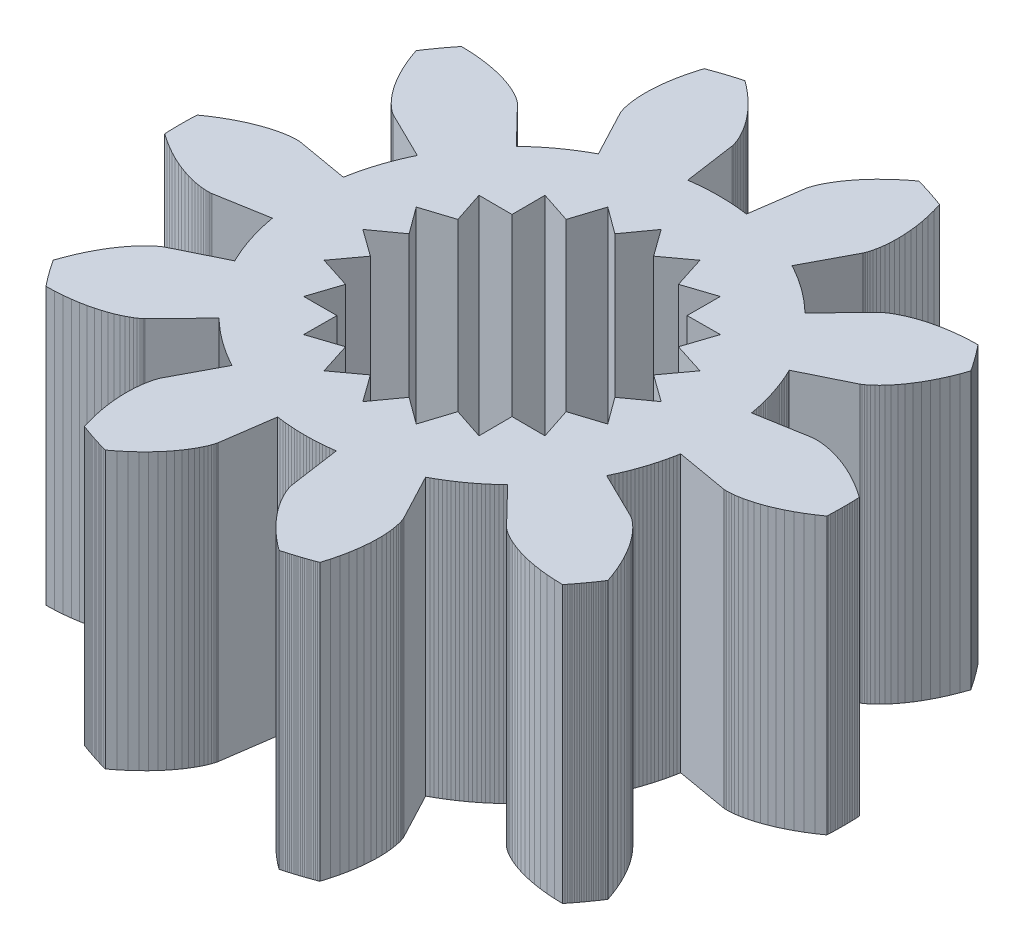
SolidWorks part; units mm, degrees
ref_plane "Front Plane" through (0, 0, 0) normal (0, 0, 1) x (1, 0, 0)
ref_plane "Top Plane" through (0, 0, 0) normal (0, 1, 0) x (1, 0, 0)
ref_plane "Right Plane" through (0, 0, 0) normal (1, 0, 0) x (0, 0, -1)
sketch "Sketch1" plane through (0, 0, 0) normal (0, 1, 0) x (1, 0, 0)
  line L0 (3.6947, -0.6418) -> (4.6291, -0.8041)
  line L1 (4.6291, -0.8041) -> (4.6332, -0.8047)
  line L2 (4.6332, -0.8047) -> (4.6455, -0.806)
  line L3 (4.6455, -0.806) -> (4.6659, -0.8073)
  line L4 (4.6659, -0.8073) -> (4.6947, -0.8081)
  line L5 (4.6947, -0.8081) -> (4.7316, -0.8074)
  line L6 (4.7316, -0.8074) -> (4.7767, -0.8048)
  line L7 (4.7767, -0.8048) -> (4.8297, -0.7994)
  line L8 (4.8297, -0.7994) -> (4.8907, -0.7907)
  line L9 (4.8907, -0.7907) -> (4.9593, -0.778)
  line L10 (4.9593, -0.778) -> (5.0353, -0.7605)
  line L11 (5.0353, -0.7605) -> (5.1184, -0.7378)
  line L12 (5.1184, -0.7378) -> (5.2084, -0.7091)
  line L13 (5.2084, -0.7091) -> (5.3047, -0.6738)
  line L14 (5.3047, -0.6738) -> (5.4071, -0.6314)
  line L15 (5.4071, -0.6314) -> (5.5151, -0.5813)
  line L16 (5.5151, -0.5813) -> (5.6282, -0.523)
  line L17 (5.6282, -0.523) -> (5.7459, -0.456)
  line L18 (5.7459, -0.456) -> (5.8676, -0.3797)
  line L19 (5.8676, -0.3797) -> (5.9928, -0.2937)
  line L20 (5.9928, -0.2937) -> (5.9942, -0.2628)
  line L21 (5.9942, -0.2628) -> (5.9955, -0.2319)
  line L22 (5.9955, -0.2319) -> (5.9966, -0.201)
  line L23 (5.9966, -0.201) -> (5.9976, -0.1701)
  line L24 (5.9976, -0.1701) -> (5.9984, -0.1392)
  line L25 (5.9984, -0.1392) -> (5.999, -0.1083)
  line L26 (5.999, -0.1083) -> (5.9995, -0.0773)
  line L27 (5.9995, -0.0773) -> (5.9998, -0.0464)
  line L28 (5.9998, -0.0464) -> (6, -0.0155)
  line L29 (6, -0.0155) -> (6, 0.0155)
  line L30 (6, 0.0155) -> (5.9998, 0.0464)
  line L31 (5.9998, 0.0464) -> (5.9995, 0.0773)
  line L32 (5.9995, 0.0773) -> (5.999, 0.1083)
  line L33 (5.999, 0.1083) -> (5.9984, 0.1392)
  line L34 (5.9984, 0.1392) -> (5.9976, 0.1701)
  line L35 (5.9976, 0.1701) -> (5.9966, 0.201)
  line L36 (5.9966, 0.201) -> (5.9955, 0.2319)
  line L37 (5.9955, 0.2319) -> (5.9942, 0.2628)
  line L38 (5.9942, 0.2628) -> (5.9928, 0.2937)
  line L39 (5.9928, 0.2937) -> (5.8676, 0.3797)
  line L40 (5.8676, 0.3797) -> (5.7459, 0.456)
  line L41 (5.7459, 0.456) -> (5.6282, 0.523)
  line L42 (5.6282, 0.523) -> (5.5151, 0.5813)
  line L43 (5.5151, 0.5813) -> (5.4071, 0.6314)
  line L44 (5.4071, 0.6314) -> (5.3047, 0.6738)
  line L45 (5.3047, 0.6738) -> (5.2084, 0.7091)
  line L46 (5.2084, 0.7091) -> (5.1184, 0.7378)
  line L47 (5.1184, 0.7378) -> (5.0353, 0.7605)
  line L48 (5.0353, 0.7605) -> (4.9593, 0.778)
  line L49 (4.9593, 0.778) -> (4.8907, 0.7907)
  line L50 (4.8907, 0.7907) -> (4.8297, 0.7994)
  line L51 (4.8297, 0.7994) -> (4.7767, 0.8048)
  line L52 (4.7767, 0.8048) -> (4.7316, 0.8074)
  line L53 (4.7316, 0.8074) -> (4.6947, 0.8081)
  line L54 (4.6947, 0.8081) -> (4.6659, 0.8073)
  line L55 (4.6659, 0.8073) -> (4.6455, 0.806)
  line L56 (4.6455, 0.806) -> (4.6332, 0.8047)
  line L57 (4.6332, 0.8047) -> (4.6291, 0.8041)
  line L58 (4.6291, 0.8041) -> (3.6947, 0.6418)
  line L59 (3.6947, 0.6418) -> (3.6847, 0.697)
  line L60 (3.6847, 0.697) -> (3.6738, 0.752)
  line L61 (3.6738, 0.752) -> (3.6621, 0.8069)
  line L62 (3.6621, 0.8069) -> (3.6497, 0.8617)
  line L63 (3.6497, 0.8617) -> (3.6364, 0.9162)
  line L64 (3.6364, 0.9162) -> (3.6222, 0.9705)
  line L65 (3.6222, 0.9705) -> (3.6073, 1.0246)
  line L66 (3.6073, 1.0246) -> (3.5916, 1.0785)
  line L67 (3.5916, 1.0785) -> (3.575, 1.1321)
  line L68 (3.575, 1.1321) -> (3.5577, 1.1855)
  line L69 (3.5577, 1.1855) -> (3.5396, 1.2386)
  line L70 (3.5396, 1.2386) -> (3.5206, 1.2914)
  line L71 (3.5206, 1.2914) -> (3.5009, 1.344)
  line L72 (3.5009, 1.344) -> (3.4804, 1.3962)
  line L73 (3.4804, 1.3962) -> (3.4591, 1.4481)
  line L74 (3.4591, 1.4481) -> (3.4371, 1.4997)
  line L75 (3.4371, 1.4997) -> (3.4142, 1.551)
  line L76 (3.4142, 1.551) -> (3.3906, 1.6019)
  line L77 (3.3906, 1.6019) -> (3.3663, 1.6525)
  line L78 (3.3663, 1.6525) -> (4.2177, 2.0704)
  line L79 (4.2177, 2.0704) -> (4.2213, 2.0723)
  line L80 (4.2213, 2.0723) -> (4.232, 2.0785)
  line L81 (4.232, 2.0785) -> (4.2494, 2.0894)
  line L82 (4.2494, 2.0894) -> (4.273, 2.1057)
  line L83 (4.273, 2.1057) -> (4.3025, 2.1279)
  line L84 (4.3025, 2.1279) -> (4.3374, 2.1566)
  line L85 (4.3374, 2.1566) -> (4.3773, 2.1921)
  line L86 (4.3773, 2.1921) -> (4.4214, 2.235)
  line L87 (4.4214, 2.235) -> (4.4694, 2.2856)
  line L88 (4.4694, 2.2856) -> (4.5207, 2.3444)
  line L89 (4.5207, 2.3444) -> (4.5746, 2.4117)
  line L90 (4.5746, 2.4117) -> (4.6304, 2.4877)
  line L91 (4.6304, 2.4877) -> (4.6877, 2.5729)
  line L92 (4.6877, 2.5729) -> (4.7456, 2.6674)
  line L93 (4.7456, 2.6674) -> (4.8035, 2.7714)
  line L94 (4.8035, 2.7714) -> (4.8607, 2.885)
  line L95 (4.8607, 2.885) -> (4.9165, 3.0085)
  line L96 (4.9165, 3.0085) -> (4.9702, 3.1417)
  line L97 (4.9702, 3.1417) -> (5.0209, 3.2848)
  line L98 (5.0209, 3.2848) -> (5.0039, 3.3107)
  line L99 (5.0039, 3.3107) -> (4.9868, 3.3364)
  line L100 (4.9868, 3.3364) -> (4.9695, 3.3621)
  line L101 (4.9695, 3.3621) -> (4.9521, 3.3877)
  line L102 (4.9521, 3.3877) -> (4.9346, 3.4132)
  line L103 (4.9346, 3.4132) -> (4.9169, 3.4386)
  line L104 (4.9169, 3.4386) -> (4.8992, 3.4639)
  line L105 (4.8992, 3.4639) -> (4.8812, 3.4891)
  line L106 (4.8812, 3.4891) -> (4.8632, 3.5142)
  line L107 (4.8632, 3.5142) -> (4.845, 3.5392)
  line L108 (4.845, 3.5392) -> (4.8267, 3.5641)
  line L109 (4.8267, 3.5641) -> (4.8082, 3.589)
  line L110 (4.8082, 3.589) -> (4.7897, 3.6137)
  line L111 (4.7897, 3.6137) -> (4.771, 3.6384)
  line L112 (4.771, 3.6384) -> (4.7522, 3.6629)
  line L113 (4.7522, 3.6629) -> (4.7332, 3.6874)
  line L114 (4.7332, 3.6874) -> (4.7141, 3.7117)
  line L115 (4.7141, 3.7117) -> (4.6949, 3.736)
  line L116 (4.6949, 3.736) -> (4.6756, 3.7601)
  line L117 (4.6756, 3.7601) -> (4.5238, 3.7561)
  line L118 (4.5238, 3.7561) -> (4.3805, 3.7462)
  line L119 (4.3805, 3.7462) -> (4.2459, 3.7313)
  line L120 (4.2459, 3.7313) -> (4.1201, 3.712)
  line L121 (4.1201, 3.712) -> (4.0033, 3.6891)
  line L122 (4.0033, 3.6891) -> (3.8956, 3.6632)
  line L123 (3.8956, 3.6632) -> (3.7969, 3.6351)
  line L124 (3.7969, 3.6351) -> (3.7072, 3.6054)
  line L125 (3.7072, 3.6054) -> (3.6266, 3.575)
  line L126 (3.6266, 3.575) -> (3.5549, 3.5444)
  line L127 (3.5549, 3.5444) -> (3.4919, 3.5144)
  line L128 (3.4919, 3.5144) -> (3.4374, 3.4856)
  line L129 (3.4374, 3.4856) -> (3.3914, 3.4587)
  line L130 (3.3914, 3.4587) -> (3.3533, 3.4344)
  line L131 (3.3533, 3.4344) -> (3.3231, 3.4132)
  line L132 (3.3231, 3.4132) -> (3.3003, 3.3957)
  line L133 (3.3003, 3.3957) -> (3.2845, 3.3826)
  line L134 (3.2845, 3.3826) -> (3.2754, 3.3743)
  line L135 (3.2754, 3.3743) -> (3.2724, 3.3715)
  line L136 (3.2724, 3.3715) -> (2.6118, 2.6909)
  line L137 (2.6118, 2.6909) -> (2.5713, 2.7297)
  line L138 (2.5713, 2.7297) -> (2.5301, 2.7678)
  line L139 (2.5301, 2.7678) -> (2.4884, 2.8054)
  line L140 (2.4884, 2.8054) -> (2.4462, 2.8423)
  line L141 (2.4462, 2.8423) -> (2.4034, 2.8786)
  line L142 (2.4034, 2.8786) -> (2.36, 2.9142)
  line L143 (2.36, 2.9142) -> (2.3161, 2.9492)
  line L144 (2.3161, 2.9492) -> (2.2717, 2.9836)
  line L145 (2.2717, 2.9836) -> (2.2268, 3.0172)
  line L146 (2.2268, 3.0172) -> (2.1814, 3.0502)
  line L147 (2.1814, 3.0502) -> (2.1355, 3.0825)
  line L148 (2.1355, 3.0825) -> (2.0892, 3.1141)
  line L149 (2.0892, 3.1141) -> (2.0423, 3.1451)
  line L150 (2.0423, 3.1451) -> (1.995, 3.1753)
  line L151 (1.995, 3.1753) -> (1.9473, 3.2048)
  line L152 (1.9473, 3.2048) -> (1.8991, 3.2336)
  line L153 (1.8991, 3.2336) -> (1.8505, 3.2616)
  line L154 (1.8505, 3.2616) -> (1.8015, 3.2889)
  line L155 (1.8015, 3.2889) -> (1.7521, 3.3155)
  line L156 (1.7521, 3.3155) -> (2.1952, 4.1541)
  line L157 (2.1952, 4.1541) -> (2.197, 4.1578)
  line L158 (2.197, 4.1578) -> (2.2021, 4.169)
  line L159 (2.2021, 4.169) -> (2.2097, 4.1881)
  line L160 (2.2097, 4.1881) -> (2.2192, 4.2152)
  line L161 (2.2192, 4.2152) -> (2.23, 4.2505)
  line L162 (2.23, 4.2505) -> (2.2415, 4.2942)
  line L163 (2.2415, 4.2942) -> (2.2528, 4.3463)
  line L164 (2.2528, 4.3463) -> (2.2633, 4.407)
  line L165 (2.2633, 4.407) -> (2.2724, 4.4762)
  line L166 (2.2724, 4.4762) -> (2.2793, 4.5538)
  line L167 (2.2793, 4.5538) -> (2.2834, 4.6399)
  line L168 (2.2834, 4.6399) -> (2.2838, 4.7343)
  line L169 (2.2838, 4.7343) -> (2.2801, 4.8369)
  line L170 (2.2801, 4.8369) -> (2.2714, 4.9474)
  line L171 (2.2714, 4.9474) -> (2.2571, 5.0655)
  line L172 (2.2571, 5.0655) -> (2.2366, 5.1911)
  line L173 (2.2366, 5.1911) -> (2.2092, 5.3237)
  line L174 (2.2092, 5.3237) -> (2.1743, 5.4631)
  line L175 (2.1743, 5.4631) -> (2.1312, 5.6087)
  line L176 (2.1312, 5.6087) -> (2.1023, 5.6196)
  line L177 (2.1023, 5.6196) -> (2.0733, 5.6304)
  line L178 (2.0733, 5.6304) -> (2.0442, 5.641)
  line L179 (2.0442, 5.641) -> (2.0151, 5.6515)
  line L180 (2.0151, 5.6515) -> (1.986, 5.6618)
  line L181 (1.986, 5.6618) -> (1.9568, 5.672)
  line L182 (1.9568, 5.672) -> (1.9275, 5.682)
  line L183 (1.9275, 5.682) -> (1.8982, 5.6918)
  line L184 (1.8982, 5.6918) -> (1.8688, 5.7015)
  line L185 (1.8688, 5.7015) -> (1.8394, 5.7111)
  line L186 (1.8394, 5.7111) -> (1.8099, 5.7205)
  line L187 (1.8099, 5.7205) -> (1.7804, 5.7298)
  line L188 (1.7804, 5.7298) -> (1.7508, 5.7389)
  line L189 (1.7508, 5.7389) -> (1.7212, 5.7478)
  line L190 (1.7212, 5.7478) -> (1.6916, 5.7566)
  line L191 (1.6916, 5.7566) -> (1.6619, 5.7653)
  line L192 (1.6619, 5.7653) -> (1.6321, 5.7737)
  line L193 (1.6321, 5.7737) -> (1.6023, 5.7821)
  line L194 (1.6023, 5.7821) -> (1.5725, 5.7903)
  line L195 (1.5725, 5.7903) -> (1.4521, 5.6977)
  line L196 (1.4521, 5.6977) -> (1.3419, 5.6055)
  line L197 (1.3419, 5.6055) -> (1.2418, 5.5143)
  line L198 (1.2418, 5.5143) -> (1.1514, 5.4248)
  line L199 (1.1514, 5.4248) -> (1.0704, 5.3376)
  line L200 (1.0704, 5.3376) -> (0.9984, 5.2533)
  line L201 (0.9984, 5.2533) -> (0.9351, 5.1726)
  line L202 (0.9351, 5.1726) -> (0.88, 5.0959)
  line L203 (0.88, 5.0959) -> (0.8327, 5.0239)
  line L204 (0.8327, 5.0239) -> (0.7926, 4.957)
  line L205 (0.7926, 4.957) -> (0.7593, 4.8957)
  line L206 (0.7593, 4.8957) -> (0.7322, 4.8404)
  line L207 (0.7322, 4.8404) -> (0.7107, 4.7916)
  line L208 (0.7107, 4.7916) -> (0.6942, 4.7495)
  line L209 (0.6942, 4.7495) -> (0.6822, 4.7146)
  line L210 (0.6822, 4.7146) -> (0.674, 4.687)
  line L211 (0.674, 4.687) -> (0.669, 4.6672)
  line L212 (0.669, 4.6672) -> (0.6665, 4.6551)
  line L213 (0.6665, 4.6551) -> (0.6658, 4.6511)
  line L214 (0.6658, 4.6511) -> (0.5314, 3.7122)
  line L215 (0.5314, 3.7122) -> (0.4757, 3.7197)
  line L216 (0.4757, 3.7197) -> (0.42, 3.7264)
  line L217 (0.42, 3.7264) -> (0.3642, 3.7323)
  line L218 (0.3642, 3.7323) -> (0.3083, 3.7373)
  line L219 (0.3083, 3.7373) -> (0.2524, 3.7415)
  line L220 (0.2524, 3.7415) -> (0.1963, 3.7449)
  line L221 (0.1963, 3.7449) -> (0.1403, 3.7474)
  line L222 (0.1403, 3.7474) -> (0.0842, 3.7491)
  line L223 (0.0842, 3.7491) -> (0.0281, 3.7499)
  line L224 (0.0281, 3.7499) -> (-0.0281, 3.7499)
  line L225 (-0.0281, 3.7499) -> (-0.0842, 3.7491)
  line L226 (-0.0842, 3.7491) -> (-0.1403, 3.7474)
  line L227 (-0.1403, 3.7474) -> (-0.1963, 3.7449)
  line L228 (-0.1963, 3.7449) -> (-0.2524, 3.7415)
  line L229 (-0.2524, 3.7415) -> (-0.3083, 3.7373)
  line L230 (-0.3083, 3.7373) -> (-0.3642, 3.7323)
  line L231 (-0.3642, 3.7323) -> (-0.42, 3.7264)
  line L232 (-0.42, 3.7264) -> (-0.4757, 3.7197)
  line L233 (-0.4757, 3.7197) -> (-0.5314, 3.7122)
  line L234 (-0.5314, 3.7122) -> (-0.6658, 4.6511)
  line L235 (-0.6658, 4.6511) -> (-0.6665, 4.6551)
  line L236 (-0.6665, 4.6551) -> (-0.669, 4.6672)
  line L237 (-0.669, 4.6672) -> (-0.674, 4.687)
  line L238 (-0.674, 4.687) -> (-0.6822, 4.7146)
  line L239 (-0.6822, 4.7146) -> (-0.6942, 4.7495)
  line L240 (-0.6942, 4.7495) -> (-0.7107, 4.7916)
  line L241 (-0.7107, 4.7916) -> (-0.7322, 4.8404)
  line L242 (-0.7322, 4.8404) -> (-0.7593, 4.8957)
  line L243 (-0.7593, 4.8957) -> (-0.7926, 4.957)
  line L244 (-0.7926, 4.957) -> (-0.8327, 5.0239)
  line L245 (-0.8327, 5.0239) -> (-0.88, 5.0959)
  line L246 (-0.88, 5.0959) -> (-0.9351, 5.1726)
  line L247 (-0.9351, 5.1726) -> (-0.9984, 5.2533)
  line L248 (-0.9984, 5.2533) -> (-1.0704, 5.3376)
  line L249 (-1.0704, 5.3376) -> (-1.1514, 5.4248)
  line L250 (-1.1514, 5.4248) -> (-1.2418, 5.5143)
  line L251 (-1.2418, 5.5143) -> (-1.3419, 5.6055)
  line L252 (-1.3419, 5.6055) -> (-1.4521, 5.6977)
  line L253 (-1.4521, 5.6977) -> (-1.5725, 5.7903)
  line L254 (-1.5725, 5.7903) -> (-1.6023, 5.7821)
  line L255 (-1.6023, 5.7821) -> (-1.6321, 5.7737)
  line L256 (-1.6321, 5.7737) -> (-1.6619, 5.7653)
  line L257 (-1.6619, 5.7653) -> (-1.6916, 5.7566)
  line L258 (-1.6916, 5.7566) -> (-1.7212, 5.7478)
  line L259 (-1.7212, 5.7478) -> (-1.7508, 5.7389)
  line L260 (-1.7508, 5.7389) -> (-1.7804, 5.7298)
  line L261 (-1.7804, 5.7298) -> (-1.8099, 5.7205)
  line L262 (-1.8099, 5.7205) -> (-1.8394, 5.7111)
  line L263 (-1.8394, 5.7111) -> (-1.8688, 5.7015)
  line L264 (-1.8688, 5.7015) -> (-1.8982, 5.6918)
  line L265 (-1.8982, 5.6918) -> (-1.9275, 5.682)
  line L266 (-1.9275, 5.682) -> (-1.9568, 5.672)
  line L267 (-1.9568, 5.672) -> (-1.986, 5.6618)
  line L268 (-1.986, 5.6618) -> (-2.0151, 5.6515)
  line L269 (-2.0151, 5.6515) -> (-2.0442, 5.641)
  line L270 (-2.0442, 5.641) -> (-2.0733, 5.6304)
  line L271 (-2.0733, 5.6304) -> (-2.1023, 5.6196)
  line L272 (-2.1023, 5.6196) -> (-2.1312, 5.6087)
  line L273 (-2.1312, 5.6087) -> (-2.1743, 5.4631)
  line L274 (-2.1743, 5.4631) -> (-2.2092, 5.3237)
  line L275 (-2.2092, 5.3237) -> (-2.2366, 5.1911)
  line L276 (-2.2366, 5.1911) -> (-2.2571, 5.0655)
  line L277 (-2.2571, 5.0655) -> (-2.2714, 4.9474)
  line L278 (-2.2714, 4.9474) -> (-2.2801, 4.8369)
  line L279 (-2.2801, 4.8369) -> (-2.2838, 4.7343)
  line L280 (-2.2838, 4.7343) -> (-2.2834, 4.6399)
  line L281 (-2.2834, 4.6399) -> (-2.2793, 4.5538)
  line L282 (-2.2793, 4.5538) -> (-2.2724, 4.4762)
  line L283 (-2.2724, 4.4762) -> (-2.2633, 4.407)
  line L284 (-2.2633, 4.407) -> (-2.2528, 4.3463)
  line L285 (-2.2528, 4.3463) -> (-2.2415, 4.2942)
  line L286 (-2.2415, 4.2942) -> (-2.23, 4.2505)
  line L287 (-2.23, 4.2505) -> (-2.2192, 4.2152)
  line L288 (-2.2192, 4.2152) -> (-2.2097, 4.1881)
  line L289 (-2.2097, 4.1881) -> (-2.2021, 4.169)
  line L290 (-2.2021, 4.169) -> (-2.197, 4.1578)
  line L291 (-2.197, 4.1578) -> (-2.1952, 4.1541)
  line L292 (-2.1952, 4.1541) -> (-1.7521, 3.3155)
  line L293 (-1.7521, 3.3155) -> (-1.8015, 3.2889)
  line L294 (-1.8015, 3.2889) -> (-1.8505, 3.2616)
  line L295 (-1.8505, 3.2616) -> (-1.8991, 3.2336)
  line L296 (-1.8991, 3.2336) -> (-1.9473, 3.2048)
  line L297 (-1.9473, 3.2048) -> (-1.995, 3.1753)
  line L298 (-1.995, 3.1753) -> (-2.0423, 3.1451)
  line L299 (-2.0423, 3.1451) -> (-2.0892, 3.1141)
  line L300 (-2.0892, 3.1141) -> (-2.1355, 3.0825)
  line L301 (-2.1355, 3.0825) -> (-2.1814, 3.0502)
  line L302 (-2.1814, 3.0502) -> (-2.2268, 3.0172)
  line L303 (-2.2268, 3.0172) -> (-2.2717, 2.9836)
  line L304 (-2.2717, 2.9836) -> (-2.3161, 2.9492)
  line L305 (-2.3161, 2.9492) -> (-2.36, 2.9142)
  line L306 (-2.36, 2.9142) -> (-2.4034, 2.8786)
  line L307 (-2.4034, 2.8786) -> (-2.4462, 2.8423)
  line L308 (-2.4462, 2.8423) -> (-2.4884, 2.8054)
  line L309 (-2.4884, 2.8054) -> (-2.5301, 2.7678)
  line L310 (-2.5301, 2.7678) -> (-2.5713, 2.7297)
  line L311 (-2.5713, 2.7297) -> (-2.6118, 2.6909)
  line L312 (-2.6118, 2.6909) -> (-3.2724, 3.3715)
  line L313 (-3.2724, 3.3715) -> (-3.2754, 3.3743)
  line L314 (-3.2754, 3.3743) -> (-3.2845, 3.3826)
  line L315 (-3.2845, 3.3826) -> (-3.3003, 3.3957)
  line L316 (-3.3003, 3.3957) -> (-3.3231, 3.4132)
  line L317 (-3.3231, 3.4132) -> (-3.3533, 3.4344)
  line L318 (-3.3533, 3.4344) -> (-3.3914, 3.4587)
  line L319 (-3.3914, 3.4587) -> (-3.4374, 3.4856)
  line L320 (-3.4374, 3.4856) -> (-3.4919, 3.5144)
  line L321 (-3.4919, 3.5144) -> (-3.5549, 3.5444)
  line L322 (-3.5549, 3.5444) -> (-3.6266, 3.575)
  line L323 (-3.6266, 3.575) -> (-3.7072, 3.6054)
  line L324 (-3.7072, 3.6054) -> (-3.7969, 3.6351)
  line L325 (-3.7969, 3.6351) -> (-3.8956, 3.6632)
  line L326 (-3.8956, 3.6632) -> (-4.0033, 3.6891)
  line L327 (-4.0033, 3.6891) -> (-4.1201, 3.712)
  line L328 (-4.1201, 3.712) -> (-4.2459, 3.7313)
  line L329 (-4.2459, 3.7313) -> (-4.3805, 3.7462)
  line L330 (-4.3805, 3.7462) -> (-4.5238, 3.7561)
  line L331 (-4.5238, 3.7561) -> (-4.6756, 3.7601)
  line L332 (-4.6756, 3.7601) -> (-4.6949, 3.736)
  line L333 (-4.6949, 3.736) -> (-4.7141, 3.7117)
  line L334 (-4.7141, 3.7117) -> (-4.7332, 3.6874)
  line L335 (-4.7332, 3.6874) -> (-4.7522, 3.6629)
  line L336 (-4.7522, 3.6629) -> (-4.771, 3.6384)
  line L337 (-4.771, 3.6384) -> (-4.7897, 3.6137)
  line L338 (-4.7897, 3.6137) -> (-4.8082, 3.589)
  line L339 (-4.8082, 3.589) -> (-4.8267, 3.5641)
  line L340 (-4.8267, 3.5641) -> (-4.845, 3.5392)
  line L341 (-4.845, 3.5392) -> (-4.8632, 3.5142)
  line L342 (-4.8632, 3.5142) -> (-4.8812, 3.4891)
  line L343 (-4.8812, 3.4891) -> (-4.8992, 3.4639)
  line L344 (-4.8992, 3.4639) -> (-4.9169, 3.4386)
  line L345 (-4.9169, 3.4386) -> (-4.9346, 3.4132)
  line L346 (-4.9346, 3.4132) -> (-4.9521, 3.3877)
  line L347 (-4.9521, 3.3877) -> (-4.9695, 3.3621)
  line L348 (-4.9695, 3.3621) -> (-4.9868, 3.3364)
  line L349 (-4.9868, 3.3364) -> (-5.0039, 3.3107)
  line L350 (-5.0039, 3.3107) -> (-5.0209, 3.2848)
  line L351 (-5.0209, 3.2848) -> (-4.9702, 3.1417)
  line L352 (-4.9702, 3.1417) -> (-4.9165, 3.0085)
  line L353 (-4.9165, 3.0085) -> (-4.8607, 2.885)
  line L354 (-4.8607, 2.885) -> (-4.8035, 2.7714)
  line L355 (-4.8035, 2.7714) -> (-4.7456, 2.6674)
  line L356 (-4.7456, 2.6674) -> (-4.6877, 2.5729)
  line L357 (-4.6877, 2.5729) -> (-4.6304, 2.4877)
  line L358 (-4.6304, 2.4877) -> (-4.5746, 2.4117)
  line L359 (-4.5746, 2.4117) -> (-4.5207, 2.3444)
  line L360 (-4.5207, 2.3444) -> (-4.4694, 2.2856)
  line L361 (-4.4694, 2.2856) -> (-4.4214, 2.235)
  line L362 (-4.4214, 2.235) -> (-4.3773, 2.1921)
  line L363 (-4.3773, 2.1921) -> (-4.3374, 2.1566)
  line L364 (-4.3374, 2.1566) -> (-4.3025, 2.1279)
  line L365 (-4.3025, 2.1279) -> (-4.273, 2.1057)
  line L366 (-4.273, 2.1057) -> (-4.2494, 2.0894)
  line L367 (-4.2494, 2.0894) -> (-4.232, 2.0785)
  line L368 (-4.232, 2.0785) -> (-4.2213, 2.0723)
  line L369 (-4.2213, 2.0723) -> (-4.2177, 2.0704)
  line L370 (-4.2177, 2.0704) -> (-3.3663, 1.6525)
  line L371 (-3.3663, 1.6525) -> (-3.3906, 1.6019)
  line L372 (-3.3906, 1.6019) -> (-3.4142, 1.551)
  line L373 (-3.4142, 1.551) -> (-3.4371, 1.4997)
  line L374 (-3.4371, 1.4997) -> (-3.4591, 1.4481)
  line L375 (-3.4591, 1.4481) -> (-3.4804, 1.3962)
  line L376 (-3.4804, 1.3962) -> (-3.5009, 1.344)
  line L377 (-3.5009, 1.344) -> (-3.5206, 1.2914)
  line L378 (-3.5206, 1.2914) -> (-3.5396, 1.2386)
  line L379 (-3.5396, 1.2386) -> (-3.5577, 1.1855)
  line L380 (-3.5577, 1.1855) -> (-3.575, 1.1321)
  line L381 (-3.575, 1.1321) -> (-3.5916, 1.0785)
  line L382 (-3.5916, 1.0785) -> (-3.6073, 1.0246)
  line L383 (-3.6073, 1.0246) -> (-3.6222, 0.9705)
  line L384 (-3.6222, 0.9705) -> (-3.6364, 0.9162)
  line L385 (-3.6364, 0.9162) -> (-3.6497, 0.8617)
  line L386 (-3.6497, 0.8617) -> (-3.6621, 0.8069)
  line L387 (-3.6621, 0.8069) -> (-3.6738, 0.752)
  line L388 (-3.6738, 0.752) -> (-3.6847, 0.697)
  line L389 (-3.6847, 0.697) -> (-3.6947, 0.6418)
  line L390 (-3.6947, 0.6418) -> (-4.6291, 0.8041)
  line L391 (-4.6291, 0.8041) -> (-4.6332, 0.8047)
  line L392 (-4.6332, 0.8047) -> (-4.6455, 0.806)
  line L393 (-4.6455, 0.806) -> (-4.6659, 0.8073)
  line L394 (-4.6659, 0.8073) -> (-4.6947, 0.8081)
  line L395 (-4.6947, 0.8081) -> (-4.7316, 0.8074)
  line L396 (-4.7316, 0.8074) -> (-4.7767, 0.8048)
  line L397 (-4.7767, 0.8048) -> (-4.8297, 0.7994)
  line L398 (-4.8297, 0.7994) -> (-4.8907, 0.7907)
  line L399 (-4.8907, 0.7907) -> (-4.9593, 0.778)
  line L400 (-4.9593, 0.778) -> (-5.0353, 0.7605)
  line L401 (-5.0353, 0.7605) -> (-5.1184, 0.7378)
  line L402 (-5.1184, 0.7378) -> (-5.2084, 0.7091)
  line L403 (-5.2084, 0.7091) -> (-5.3047, 0.6738)
  line L404 (-5.3047, 0.6738) -> (-5.4071, 0.6314)
  line L405 (-5.4071, 0.6314) -> (-5.5151, 0.5813)
  line L406 (-5.5151, 0.5813) -> (-5.6282, 0.523)
  line L407 (-5.6282, 0.523) -> (-5.7459, 0.456)
  line L408 (-5.7459, 0.456) -> (-5.8676, 0.3797)
  line L409 (-5.8676, 0.3797) -> (-5.9928, 0.2937)
  line L410 (-5.9928, 0.2937) -> (-5.9942, 0.2628)
  line L411 (-5.9942, 0.2628) -> (-5.9955, 0.2319)
  line L412 (-5.9955, 0.2319) -> (-5.9966, 0.201)
  line L413 (-5.9966, 0.201) -> (-5.9976, 0.1701)
  line L414 (-5.9976, 0.1701) -> (-5.9984, 0.1392)
  line L415 (-5.9984, 0.1392) -> (-5.999, 0.1083)
  line L416 (-5.999, 0.1083) -> (-5.9995, 0.0773)
  line L417 (-5.9995, 0.0773) -> (-5.9998, 0.0464)
  line L418 (-5.9998, 0.0464) -> (-6, 0.0155)
  line L419 (-6, 0.0155) -> (-6, -0.0155)
  line L420 (-6, -0.0155) -> (-5.9998, -0.0464)
  line L421 (-5.9998, -0.0464) -> (-5.9995, -0.0773)
  line L422 (-5.9995, -0.0773) -> (-5.999, -0.1083)
  line L423 (-5.999, -0.1083) -> (-5.9984, -0.1392)
  line L424 (-5.9984, -0.1392) -> (-5.9976, -0.1701)
  line L425 (-5.9976, -0.1701) -> (-5.9966, -0.201)
  line L426 (-5.9966, -0.201) -> (-5.9955, -0.2319)
  line L427 (-5.9955, -0.2319) -> (-5.9942, -0.2628)
  line L428 (-5.9942, -0.2628) -> (-5.9928, -0.2937)
  line L429 (-5.9928, -0.2937) -> (-5.8676, -0.3797)
  line L430 (-5.8676, -0.3797) -> (-5.7459, -0.456)
  line L431 (-5.7459, -0.456) -> (-5.6282, -0.523)
  line L432 (-5.6282, -0.523) -> (-5.5151, -0.5813)
  line L433 (-5.5151, -0.5813) -> (-5.4071, -0.6314)
  line L434 (-5.4071, -0.6314) -> (-5.3047, -0.6738)
  line L435 (-5.3047, -0.6738) -> (-5.2084, -0.7091)
  line L436 (-5.2084, -0.7091) -> (-5.1184, -0.7378)
  line L437 (-5.1184, -0.7378) -> (-5.0353, -0.7605)
  line L438 (-5.0353, -0.7605) -> (-4.9593, -0.778)
  line L439 (-4.9593, -0.778) -> (-4.8907, -0.7907)
  line L440 (-4.8907, -0.7907) -> (-4.8297, -0.7994)
  line L441 (-4.8297, -0.7994) -> (-4.7767, -0.8048)
  line L442 (-4.7767, -0.8048) -> (-4.7316, -0.8074)
  line L443 (-4.7316, -0.8074) -> (-4.6947, -0.8081)
  line L444 (-4.6947, -0.8081) -> (-4.6659, -0.8073)
  line L445 (-4.6659, -0.8073) -> (-4.6455, -0.806)
  line L446 (-4.6455, -0.806) -> (-4.6332, -0.8047)
  line L447 (-4.6332, -0.8047) -> (-4.6291, -0.8041)
  line L448 (-4.6291, -0.8041) -> (-3.6947, -0.6418)
  line L449 (-3.6947, -0.6418) -> (-3.6847, -0.697)
  line L450 (-3.6847, -0.697) -> (-3.6738, -0.752)
  line L451 (-3.6738, -0.752) -> (-3.6621, -0.8069)
  line L452 (-3.6621, -0.8069) -> (-3.6497, -0.8617)
  line L453 (-3.6497, -0.8617) -> (-3.6364, -0.9162)
  line L454 (-3.6364, -0.9162) -> (-3.6222, -0.9705)
  line L455 (-3.6222, -0.9705) -> (-3.6073, -1.0246)
  line L456 (-3.6073, -1.0246) -> (-3.5916, -1.0785)
  line L457 (-3.5916, -1.0785) -> (-3.575, -1.1321)
  line L458 (-3.575, -1.1321) -> (-3.5577, -1.1855)
  line L459 (-3.5577, -1.1855) -> (-3.5396, -1.2386)
  line L460 (-3.5396, -1.2386) -> (-3.5206, -1.2914)
  line L461 (-3.5206, -1.2914) -> (-3.5009, -1.344)
  line L462 (-3.5009, -1.344) -> (-3.4804, -1.3962)
  line L463 (-3.4804, -1.3962) -> (-3.4591, -1.4481)
  line L464 (-3.4591, -1.4481) -> (-3.4371, -1.4997)
  line L465 (-3.4371, -1.4997) -> (-3.4142, -1.551)
  line L466 (-3.4142, -1.551) -> (-3.3906, -1.6019)
  line L467 (-3.3906, -1.6019) -> (-3.3663, -1.6525)
  line L468 (-3.3663, -1.6525) -> (-4.2177, -2.0704)
  line L469 (-4.2177, -2.0704) -> (-4.2213, -2.0723)
  line L470 (-4.2213, -2.0723) -> (-4.232, -2.0785)
  line L471 (-4.232, -2.0785) -> (-4.2494, -2.0894)
  line L472 (-4.2494, -2.0894) -> (-4.273, -2.1057)
  line L473 (-4.273, -2.1057) -> (-4.3025, -2.1279)
  line L474 (-4.3025, -2.1279) -> (-4.3374, -2.1566)
  line L475 (-4.3374, -2.1566) -> (-4.3773, -2.1921)
  line L476 (-4.3773, -2.1921) -> (-4.4214, -2.235)
  line L477 (-4.4214, -2.235) -> (-4.4694, -2.2856)
  line L478 (-4.4694, -2.2856) -> (-4.5207, -2.3444)
  line L479 (-4.5207, -2.3444) -> (-4.5746, -2.4117)
  line L480 (-4.5746, -2.4117) -> (-4.6304, -2.4877)
  line L481 (-4.6304, -2.4877) -> (-4.6877, -2.5729)
  line L482 (-4.6877, -2.5729) -> (-4.7456, -2.6674)
  line L483 (-4.7456, -2.6674) -> (-4.8035, -2.7714)
  line L484 (-4.8035, -2.7714) -> (-4.8607, -2.885)
  line L485 (-4.8607, -2.885) -> (-4.9165, -3.0085)
  line L486 (-4.9165, -3.0085) -> (-4.9702, -3.1417)
  line L487 (-4.9702, -3.1417) -> (-5.0209, -3.2848)
  line L488 (-5.0209, -3.2848) -> (-5.0039, -3.3107)
  line L489 (-5.0039, -3.3107) -> (-4.9868, -3.3364)
  line L490 (-4.9868, -3.3364) -> (-4.9695, -3.3621)
  line L491 (-4.9695, -3.3621) -> (-4.9521, -3.3877)
  line L492 (-4.9521, -3.3877) -> (-4.9346, -3.4132)
  line L493 (-4.9346, -3.4132) -> (-4.9169, -3.4386)
  line L494 (-4.9169, -3.4386) -> (-4.8992, -3.4639)
  line L495 (-4.8992, -3.4639) -> (-4.8812, -3.4891)
  line L496 (-4.8812, -3.4891) -> (-4.8632, -3.5142)
  line L497 (-4.8632, -3.5142) -> (-4.845, -3.5392)
  line L498 (-4.845, -3.5392) -> (-4.8267, -3.5641)
  line L499 (-4.8267, -3.5641) -> (-4.8082, -3.589)
  line L500 (-4.8082, -3.589) -> (-4.7897, -3.6137)
  line L501 (-4.7897, -3.6137) -> (-4.771, -3.6384)
  line L502 (-4.771, -3.6384) -> (-4.7522, -3.6629)
  line L503 (-4.7522, -3.6629) -> (-4.7332, -3.6874)
  line L504 (-4.7332, -3.6874) -> (-4.7141, -3.7117)
  line L505 (-4.7141, -3.7117) -> (-4.6949, -3.736)
  line L506 (-4.6949, -3.736) -> (-4.6756, -3.7601)
  line L507 (-4.6756, -3.7601) -> (-4.5238, -3.7561)
  line L508 (-4.5238, -3.7561) -> (-4.3805, -3.7462)
  line L509 (-4.3805, -3.7462) -> (-4.2459, -3.7313)
  line L510 (-4.2459, -3.7313) -> (-4.1201, -3.712)
  line L511 (-4.1201, -3.712) -> (-4.0033, -3.6891)
  line L512 (-4.0033, -3.6891) -> (-3.8956, -3.6632)
  line L513 (-3.8956, -3.6632) -> (-3.7969, -3.6351)
  line L514 (-3.7969, -3.6351) -> (-3.7072, -3.6054)
  line L515 (-3.7072, -3.6054) -> (-3.6266, -3.575)
  line L516 (-3.6266, -3.575) -> (-3.5549, -3.5444)
  line L517 (-3.5549, -3.5444) -> (-3.4919, -3.5144)
  line L518 (-3.4919, -3.5144) -> (-3.4374, -3.4856)
  line L519 (-3.4374, -3.4856) -> (-3.3914, -3.4587)
  line L520 (-3.3914, -3.4587) -> (-3.3533, -3.4344)
  line L521 (-3.3533, -3.4344) -> (-3.3231, -3.4132)
  line L522 (-3.3231, -3.4132) -> (-3.3003, -3.3957)
  line L523 (-3.3003, -3.3957) -> (-3.2845, -3.3826)
  line L524 (-3.2845, -3.3826) -> (-3.2754, -3.3743)
  line L525 (-3.2754, -3.3743) -> (-3.2724, -3.3715)
  line L526 (-3.2724, -3.3715) -> (-2.6118, -2.6909)
  line L527 (-2.6118, -2.6909) -> (-2.5713, -2.7297)
  line L528 (-2.5713, -2.7297) -> (-2.5301, -2.7678)
  line L529 (-2.5301, -2.7678) -> (-2.4884, -2.8054)
  line L530 (-2.4884, -2.8054) -> (-2.4462, -2.8423)
  line L531 (-2.4462, -2.8423) -> (-2.4034, -2.8786)
  line L532 (-2.4034, -2.8786) -> (-2.36, -2.9142)
  line L533 (-2.36, -2.9142) -> (-2.3161, -2.9492)
  line L534 (-2.3161, -2.9492) -> (-2.2717, -2.9836)
  line L535 (-2.2717, -2.9836) -> (-2.2268, -3.0172)
  line L536 (-2.2268, -3.0172) -> (-2.1814, -3.0502)
  line L537 (-2.1814, -3.0502) -> (-2.1355, -3.0825)
  line L538 (-2.1355, -3.0825) -> (-2.0892, -3.1141)
  line L539 (-2.0892, -3.1141) -> (-2.0423, -3.1451)
  line L540 (-2.0423, -3.1451) -> (-1.995, -3.1753)
  line L541 (-1.995, -3.1753) -> (-1.9473, -3.2048)
  line L542 (-1.9473, -3.2048) -> (-1.8991, -3.2336)
  line L543 (-1.8991, -3.2336) -> (-1.8505, -3.2616)
  line L544 (-1.8505, -3.2616) -> (-1.8015, -3.2889)
  line L545 (-1.8015, -3.2889) -> (-1.7521, -3.3155)
  line L546 (-1.7521, -3.3155) -> (-2.1952, -4.1541)
  line L547 (-2.1952, -4.1541) -> (-2.197, -4.1578)
  line L548 (-2.197, -4.1578) -> (-2.2021, -4.169)
  line L549 (-2.2021, -4.169) -> (-2.2097, -4.1881)
  line L550 (-2.2097, -4.1881) -> (-2.2192, -4.2152)
  line L551 (-2.2192, -4.2152) -> (-2.23, -4.2505)
  line L552 (-2.23, -4.2505) -> (-2.2415, -4.2942)
  line L553 (-2.2415, -4.2942) -> (-2.2528, -4.3463)
  line L554 (-2.2528, -4.3463) -> (-2.2633, -4.407)
  line L555 (-2.2633, -4.407) -> (-2.2724, -4.4762)
  line L556 (-2.2724, -4.4762) -> (-2.2793, -4.5538)
  line L557 (-2.2793, -4.5538) -> (-2.2834, -4.6399)
  line L558 (-2.2834, -4.6399) -> (-2.2838, -4.7343)
  line L559 (-2.2838, -4.7343) -> (-2.2801, -4.8369)
  line L560 (-2.2801, -4.8369) -> (-2.2714, -4.9474)
  line L561 (-2.2714, -4.9474) -> (-2.2571, -5.0655)
  line L562 (-2.2571, -5.0655) -> (-2.2366, -5.1911)
  line L563 (-2.2366, -5.1911) -> (-2.2092, -5.3237)
  line L564 (-2.2092, -5.3237) -> (-2.1743, -5.4631)
  line L565 (-2.1743, -5.4631) -> (-2.1312, -5.6087)
  line L566 (-2.1312, -5.6087) -> (-2.1023, -5.6196)
  line L567 (-2.1023, -5.6196) -> (-2.0733, -5.6304)
  line L568 (-2.0733, -5.6304) -> (-2.0442, -5.641)
  line L569 (-2.0442, -5.641) -> (-2.0151, -5.6515)
  line L570 (-2.0151, -5.6515) -> (-1.986, -5.6618)
  line L571 (-1.986, -5.6618) -> (-1.9568, -5.672)
  line L572 (-1.9568, -5.672) -> (-1.9275, -5.682)
  line L573 (-1.9275, -5.682) -> (-1.8982, -5.6918)
  line L574 (-1.8982, -5.6918) -> (-1.8688, -5.7015)
  line L575 (-1.8688, -5.7015) -> (-1.8394, -5.7111)
  line L576 (-1.8394, -5.7111) -> (-1.8099, -5.7205)
  line L577 (-1.8099, -5.7205) -> (-1.7804, -5.7298)
  line L578 (-1.7804, -5.7298) -> (-1.7508, -5.7389)
  line L579 (-1.7508, -5.7389) -> (-1.7212, -5.7478)
  line L580 (-1.7212, -5.7478) -> (-1.6916, -5.7566)
  line L581 (-1.6916, -5.7566) -> (-1.6619, -5.7653)
  line L582 (-1.6619, -5.7653) -> (-1.6321, -5.7737)
  line L583 (-1.6321, -5.7737) -> (-1.6023, -5.7821)
  line L584 (-1.6023, -5.7821) -> (-1.5725, -5.7903)
  line L585 (-1.5725, -5.7903) -> (-1.4521, -5.6977)
  line L586 (-1.4521, -5.6977) -> (-1.3419, -5.6055)
  line L587 (-1.3419, -5.6055) -> (-1.2418, -5.5143)
  line L588 (-1.2418, -5.5143) -> (-1.1514, -5.4248)
  line L589 (-1.1514, -5.4248) -> (-1.0704, -5.3376)
  line L590 (-1.0704, -5.3376) -> (-0.9984, -5.2533)
  line L591 (-0.9984, -5.2533) -> (-0.9351, -5.1726)
  line L592 (-0.9351, -5.1726) -> (-0.88, -5.0959)
  line L593 (-0.88, -5.0959) -> (-0.8327, -5.0239)
  line L594 (-0.8327, -5.0239) -> (-0.7926, -4.957)
  line L595 (-0.7926, -4.957) -> (-0.7593, -4.8957)
  line L596 (-0.7593, -4.8957) -> (-0.7322, -4.8404)
  line L597 (-0.7322, -4.8404) -> (-0.7107, -4.7916)
  line L598 (-0.7107, -4.7916) -> (-0.6942, -4.7495)
  line L599 (-0.6942, -4.7495) -> (-0.6822, -4.7146)
  line L600 (-0.6822, -4.7146) -> (-0.674, -4.687)
  line L601 (-0.674, -4.687) -> (-0.669, -4.6672)
  line L602 (-0.669, -4.6672) -> (-0.6665, -4.6551)
  line L603 (-0.6665, -4.6551) -> (-0.6658, -4.6511)
  line L604 (-0.6658, -4.6511) -> (-0.5314, -3.7122)
  line L605 (-0.5314, -3.7122) -> (-0.4757, -3.7197)
  line L606 (-0.4757, -3.7197) -> (-0.42, -3.7264)
  line L607 (-0.42, -3.7264) -> (-0.3642, -3.7323)
  line L608 (-0.3642, -3.7323) -> (-0.3083, -3.7373)
  line L609 (-0.3083, -3.7373) -> (-0.2524, -3.7415)
  line L610 (-0.2524, -3.7415) -> (-0.1963, -3.7449)
  line L611 (-0.1963, -3.7449) -> (-0.1403, -3.7474)
  line L612 (-0.1403, -3.7474) -> (-0.0842, -3.7491)
  line L613 (-0.0842, -3.7491) -> (-0.0281, -3.7499)
  line L614 (-0.0281, -3.7499) -> (0.0281, -3.7499)
  line L615 (0.0281, -3.7499) -> (0.0842, -3.7491)
  line L616 (0.0842, -3.7491) -> (0.1403, -3.7474)
  line L617 (0.1403, -3.7474) -> (0.1963, -3.7449)
  line L618 (0.1963, -3.7449) -> (0.2524, -3.7415)
  line L619 (0.2524, -3.7415) -> (0.3083, -3.7373)
  line L620 (0.3083, -3.7373) -> (0.3642, -3.7323)
  line L621 (0.3642, -3.7323) -> (0.42, -3.7264)
  line L622 (0.42, -3.7264) -> (0.4757, -3.7197)
  line L623 (0.4757, -3.7197) -> (0.5314, -3.7122)
  line L624 (0.5314, -3.7122) -> (0.6658, -4.6511)
  line L625 (0.6658, -4.6511) -> (0.6665, -4.6551)
  line L626 (0.6665, -4.6551) -> (0.669, -4.6672)
  line L627 (0.669, -4.6672) -> (0.674, -4.687)
  line L628 (0.674, -4.687) -> (0.6822, -4.7146)
  line L629 (0.6822, -4.7146) -> (0.6942, -4.7495)
  line L630 (0.6942, -4.7495) -> (0.7107, -4.7916)
  line L631 (0.7107, -4.7916) -> (0.7322, -4.8404)
  line L632 (0.7322, -4.8404) -> (0.7593, -4.8957)
  line L633 (0.7593, -4.8957) -> (0.7926, -4.957)
  line L634 (0.7926, -4.957) -> (0.8327, -5.0239)
  line L635 (0.8327, -5.0239) -> (0.88, -5.0959)
  line L636 (0.88, -5.0959) -> (0.9351, -5.1726)
  line L637 (0.9351, -5.1726) -> (0.9984, -5.2533)
  line L638 (0.9984, -5.2533) -> (1.0704, -5.3376)
  line L639 (1.0704, -5.3376) -> (1.1514, -5.4248)
  line L640 (1.1514, -5.4248) -> (1.2418, -5.5143)
  line L641 (1.2418, -5.5143) -> (1.3419, -5.6055)
  line L642 (1.3419, -5.6055) -> (1.4521, -5.6977)
  line L643 (1.4521, -5.6977) -> (1.5725, -5.7903)
  line L644 (1.5725, -5.7903) -> (1.6023, -5.7821)
  line L645 (1.6023, -5.7821) -> (1.6321, -5.7737)
  line L646 (1.6321, -5.7737) -> (1.6619, -5.7653)
  line L647 (1.6619, -5.7653) -> (1.6916, -5.7566)
  line L648 (1.6916, -5.7566) -> (1.7212, -5.7478)
  line L649 (1.7212, -5.7478) -> (1.7508, -5.7389)
  line L650 (1.7508, -5.7389) -> (1.7804, -5.7298)
  line L651 (1.7804, -5.7298) -> (1.8099, -5.7205)
  line L652 (1.8099, -5.7205) -> (1.8394, -5.7111)
  line L653 (1.8394, -5.7111) -> (1.8688, -5.7015)
  line L654 (1.8688, -5.7015) -> (1.8982, -5.6918)
  line L655 (1.8982, -5.6918) -> (1.9275, -5.682)
  line L656 (1.9275, -5.682) -> (1.9568, -5.672)
  line L657 (1.9568, -5.672) -> (1.986, -5.6618)
  line L658 (1.986, -5.6618) -> (2.0151, -5.6515)
  line L659 (2.0151, -5.6515) -> (2.0442, -5.641)
  line L660 (2.0442, -5.641) -> (2.0733, -5.6304)
  line L661 (2.0733, -5.6304) -> (2.1023, -5.6196)
  line L662 (2.1023, -5.6196) -> (2.1312, -5.6087)
  line L663 (2.1312, -5.6087) -> (2.1743, -5.4631)
  line L664 (2.1743, -5.4631) -> (2.2092, -5.3237)
  line L665 (2.2092, -5.3237) -> (2.2366, -5.1911)
  line L666 (2.2366, -5.1911) -> (2.2571, -5.0655)
  line L667 (2.2571, -5.0655) -> (2.2714, -4.9474)
  line L668 (2.2714, -4.9474) -> (2.2801, -4.8369)
  line L669 (2.2801, -4.8369) -> (2.2838, -4.7343)
  line L670 (2.2838, -4.7343) -> (2.2834, -4.6399)
  line L671 (2.2834, -4.6399) -> (2.2793, -4.5538)
  line L672 (2.2793, -4.5538) -> (2.2724, -4.4762)
  line L673 (2.2724, -4.4762) -> (2.2633, -4.407)
  line L674 (2.2633, -4.407) -> (2.2528, -4.3463)
  line L675 (2.2528, -4.3463) -> (2.2415, -4.2942)
  line L676 (2.2415, -4.2942) -> (2.23, -4.2505)
  line L677 (2.23, -4.2505) -> (2.2192, -4.2152)
  line L678 (2.2192, -4.2152) -> (2.2097, -4.1881)
  line L679 (2.2097, -4.1881) -> (2.2021, -4.169)
  line L680 (2.2021, -4.169) -> (2.197, -4.1578)
  line L681 (2.197, -4.1578) -> (2.1952, -4.1541)
  line L682 (2.1952, -4.1541) -> (1.7521, -3.3155)
  line L683 (1.7521, -3.3155) -> (1.8015, -3.2889)
  line L684 (1.8015, -3.2889) -> (1.8505, -3.2616)
  line L685 (1.8505, -3.2616) -> (1.8991, -3.2336)
  line L686 (1.8991, -3.2336) -> (1.9473, -3.2048)
  line L687 (1.9473, -3.2048) -> (1.995, -3.1753)
  line L688 (1.995, -3.1753) -> (2.0423, -3.1451)
  line L689 (2.0423, -3.1451) -> (2.0892, -3.1141)
  line L690 (2.0892, -3.1141) -> (2.1355, -3.0825)
  line L691 (2.1355, -3.0825) -> (2.1814, -3.0502)
  line L692 (2.1814, -3.0502) -> (2.2268, -3.0172)
  line L693 (2.2268, -3.0172) -> (2.2717, -2.9836)
  line L694 (2.2717, -2.9836) -> (2.3161, -2.9492)
  line L695 (2.3161, -2.9492) -> (2.36, -2.9142)
  line L696 (2.36, -2.9142) -> (2.4034, -2.8786)
  line L697 (2.4034, -2.8786) -> (2.4462, -2.8423)
  line L698 (2.4462, -2.8423) -> (2.4884, -2.8054)
  line L699 (2.4884, -2.8054) -> (2.5301, -2.7678)
  line L700 (2.5301, -2.7678) -> (2.5713, -2.7297)
  line L701 (2.5713, -2.7297) -> (2.6118, -2.6909)
  line L702 (2.6118, -2.6909) -> (3.2724, -3.3715)
  line L703 (3.2724, -3.3715) -> (3.2754, -3.3743)
  line L704 (3.2754, -3.3743) -> (3.2845, -3.3826)
  line L705 (3.2845, -3.3826) -> (3.3003, -3.3957)
  line L706 (3.3003, -3.3957) -> (3.3231, -3.4132)
  line L707 (3.3231, -3.4132) -> (3.3533, -3.4344)
  line L708 (3.3533, -3.4344) -> (3.3914, -3.4587)
  line L709 (3.3914, -3.4587) -> (3.4374, -3.4856)
  line L710 (3.4374, -3.4856) -> (3.4919, -3.5144)
  line L711 (3.4919, -3.5144) -> (3.5549, -3.5444)
  line L712 (3.5549, -3.5444) -> (3.6266, -3.575)
  line L713 (3.6266, -3.575) -> (3.7072, -3.6054)
  line L714 (3.7072, -3.6054) -> (3.7969, -3.6351)
  line L715 (3.7969, -3.6351) -> (3.8956, -3.6632)
  line L716 (3.8956, -3.6632) -> (4.0033, -3.6891)
  line L717 (4.0033, -3.6891) -> (4.1201, -3.712)
  line L718 (4.1201, -3.712) -> (4.2459, -3.7313)
  line L719 (4.2459, -3.7313) -> (4.3805, -3.7462)
  line L720 (4.3805, -3.7462) -> (4.5238, -3.7561)
  line L721 (4.5238, -3.7561) -> (4.6756, -3.7601)
  line L722 (4.6756, -3.7601) -> (4.6949, -3.736)
  line L723 (4.6949, -3.736) -> (4.7141, -3.7117)
  line L724 (4.7141, -3.7117) -> (4.7332, -3.6874)
  line L725 (4.7332, -3.6874) -> (4.7522, -3.6629)
  line L726 (4.7522, -3.6629) -> (4.771, -3.6384)
  line L727 (4.771, -3.6384) -> (4.7897, -3.6137)
  line L728 (4.7897, -3.6137) -> (4.8082, -3.589)
  line L729 (4.8082, -3.589) -> (4.8267, -3.5641)
  line L730 (4.8267, -3.5641) -> (4.845, -3.5392)
  line L731 (4.845, -3.5392) -> (4.8632, -3.5142)
  line L732 (4.8632, -3.5142) -> (4.8812, -3.4891)
  line L733 (4.8812, -3.4891) -> (4.8992, -3.4639)
  line L734 (4.8992, -3.4639) -> (4.9169, -3.4386)
  line L735 (4.9169, -3.4386) -> (4.9346, -3.4132)
  line L736 (4.9346, -3.4132) -> (4.9521, -3.3877)
  line L737 (4.9521, -3.3877) -> (4.9695, -3.3621)
  line L738 (4.9695, -3.3621) -> (4.9868, -3.3364)
  line L739 (4.9868, -3.3364) -> (5.0039, -3.3107)
  line L740 (5.0039, -3.3107) -> (5.0209, -3.2848)
  line L741 (5.0209, -3.2848) -> (4.9702, -3.1417)
  line L742 (4.9702, -3.1417) -> (4.9165, -3.0085)
  line L743 (4.9165, -3.0085) -> (4.8607, -2.885)
  line L744 (4.8607, -2.885) -> (4.8035, -2.7714)
  line L745 (4.8035, -2.7714) -> (4.7456, -2.6674)
  line L746 (4.7456, -2.6674) -> (4.6877, -2.5729)
  line L747 (4.6877, -2.5729) -> (4.6304, -2.4877)
  line L748 (4.6304, -2.4877) -> (4.5746, -2.4117)
  line L749 (4.5746, -2.4117) -> (4.5207, -2.3444)
  line L750 (4.5207, -2.3444) -> (4.4694, -2.2856)
  line L751 (4.4694, -2.2856) -> (4.4214, -2.235)
  line L752 (4.4214, -2.235) -> (4.3773, -2.1921)
  line L753 (4.3773, -2.1921) -> (4.3374, -2.1566)
  line L754 (4.3374, -2.1566) -> (4.3025, -2.1279)
  line L755 (4.3025, -2.1279) -> (4.273, -2.1057)
  line L756 (4.273, -2.1057) -> (4.2494, -2.0894)
  line L757 (4.2494, -2.0894) -> (4.232, -2.0785)
  line L758 (4.232, -2.0785) -> (4.2213, -2.0723)
  line L759 (4.2213, -2.0723) -> (4.2177, -2.0704)
  line L760 (4.2177, -2.0704) -> (3.3663, -1.6525)
  line L761 (3.3663, -1.6525) -> (3.3906, -1.6019)
  line L762 (3.3906, -1.6019) -> (3.4142, -1.551)
  line L763 (3.4142, -1.551) -> (3.4371, -1.4997)
  line L764 (3.4371, -1.4997) -> (3.4591, -1.4481)
  line L765 (3.4591, -1.4481) -> (3.4804, -1.3962)
  line L766 (3.4804, -1.3962) -> (3.5009, -1.344)
  line L767 (3.5009, -1.344) -> (3.5206, -1.2914)
  line L768 (3.5206, -1.2914) -> (3.5396, -1.2386)
  line L769 (3.5396, -1.2386) -> (3.5577, -1.1855)
  line L770 (3.5577, -1.1855) -> (3.575, -1.1321)
  line L771 (3.575, -1.1321) -> (3.5916, -1.0785)
  line L772 (3.5916, -1.0785) -> (3.6073, -1.0246)
  line L773 (3.6073, -1.0246) -> (3.6222, -0.9705)
  line L774 (3.6222, -0.9705) -> (3.6364, -0.9162)
  line L775 (3.6364, -0.9162) -> (3.6497, -0.8617)
  line L776 (3.6497, -0.8617) -> (3.6621, -0.8069)
  line L777 (3.6621, -0.8069) -> (3.6738, -0.752)
  line L778 (3.6738, -0.752) -> (3.6847, -0.697)
  line L779 (3.6847, -0.697) -> (3.6947, -0.6418)
extrude "Boss-Extrude1" add sketch "Sketch1" along normal blind 5
sketch "Sketch2" plane through (0, 5, 0) normal (0, 1, 0) x (1, 0, 0)
  circle A0 centre (0, 0) radius 1.5
  dimension "D1" = 3
extrude "Cut-Extrude1" cut sketch "Sketch2" against normal through all
sketch "Sketch3" plane through (0, 5, 0) normal (0, 1, 0) x (1, 0, 0)
  circle A0 centre (0, 0) radius 5
  dimension "D1" = 10
sketch "Sketch4" plane through (0, 5, 0) normal (0, 1, 0) x (1, 0, 0)
  line L0 (0, 2.7) -> (0, -2.7) construction
  line L1 (-0.3505, 2.213) -> (0, 2.7)
  line L2 (0, 2.7) -> (0.3505, 2.213)
  line L3 (0.3505, 2.213) -> (0.8343, 2.5679)
  line L4 (0.8343, 2.5679) -> (1.0172, 1.9964)
  line L5 (1.0172, 1.9964) -> (1.587, 2.1843)
  line L6 (1.587, 2.1843) -> (1.5844, 1.5844)
  line L7 (1.5844, 1.5844) -> (2.1843, 1.587)
  line L8 (2.1843, 1.587) -> (1.9964, 1.0172)
  line L9 (1.9964, 1.0172) -> (2.5679, 0.8343)
  line L10 (2.5679, 0.8343) -> (2.213, 0.3505)
  line L11 (2.213, 0.3505) -> (2.7, 0)
  line L12 (2.7, 0) -> (2.213, -0.3505)
  line L13 (2.213, -0.3505) -> (2.5679, -0.8343)
  line L14 (2.5679, -0.8343) -> (1.9964, -1.0172)
  line L15 (1.9964, -1.0172) -> (2.1843, -1.587)
  line L16 (2.1843, -1.587) -> (1.5844, -1.5844)
  line L17 (1.5844, -1.5844) -> (1.587, -2.1843)
  line L18 (1.587, -2.1843) -> (1.0172, -1.9964)
  line L19 (1.0172, -1.9964) -> (0.8343, -2.5679)
  line L20 (0.8343, -2.5679) -> (0.3505, -2.213)
  line L21 (0.3505, -2.213) -> (0, -2.7)
  line L22 (0, -2.7) -> (-0.3505, -2.213)
  line L23 (-0.3505, -2.213) -> (-0.8343, -2.5679)
  line L24 (-0.8343, -2.5679) -> (-1.0172, -1.9964)
  line L25 (-1.0172, -1.9964) -> (-1.587, -2.1843)
  line L26 (-1.587, -2.1843) -> (-1.5844, -1.5844)
  line L27 (-1.5844, -1.5844) -> (-2.1843, -1.587)
  line L28 (-2.1843, -1.587) -> (-1.9964, -1.0172)
  line L29 (-1.9964, -1.0172) -> (-2.5679, -0.8343)
  line L30 (-2.5679, -0.8343) -> (-2.213, -0.3505)
  line L31 (-2.213, -0.3505) -> (-2.7, 0)
  line L32 (-2.7, 0) -> (-2.213, 0.3505)
  line L33 (-2.213, 0.3505) -> (-2.5679, 0.8343)
  line L34 (-2.5679, 0.8343) -> (-1.9964, 1.0172)
  line L35 (-1.9964, 1.0172) -> (-2.1843, 1.587)
  line L36 (-2.1843, 1.587) -> (-1.5844, 1.5844)
  line L37 (-1.5844, 1.5844) -> (-1.587, 2.1843)
  line L38 (-1.587, 2.1843) -> (-1.0172, 1.9964)
  line L39 (-1.0172, 1.9964) -> (-0.8343, 2.5679)
  line L40 (-0.8343, 2.5679) -> (-0.3505, 2.213)
  point P63 (0, 0)
  dimension "D1" = 5.4
  dimension "D2" = 0.6
  dimension "D3" = 20
extrude "Cut-Extrude2" cut sketch "Sketch4" against normal through all
sketch "Sketch5" plane through (0, 0, 0) normal (0, -1, 0) x (1, 0, 0)
  circle A0 centre (0, 0) radius 5
  dimension "D1" = 10
